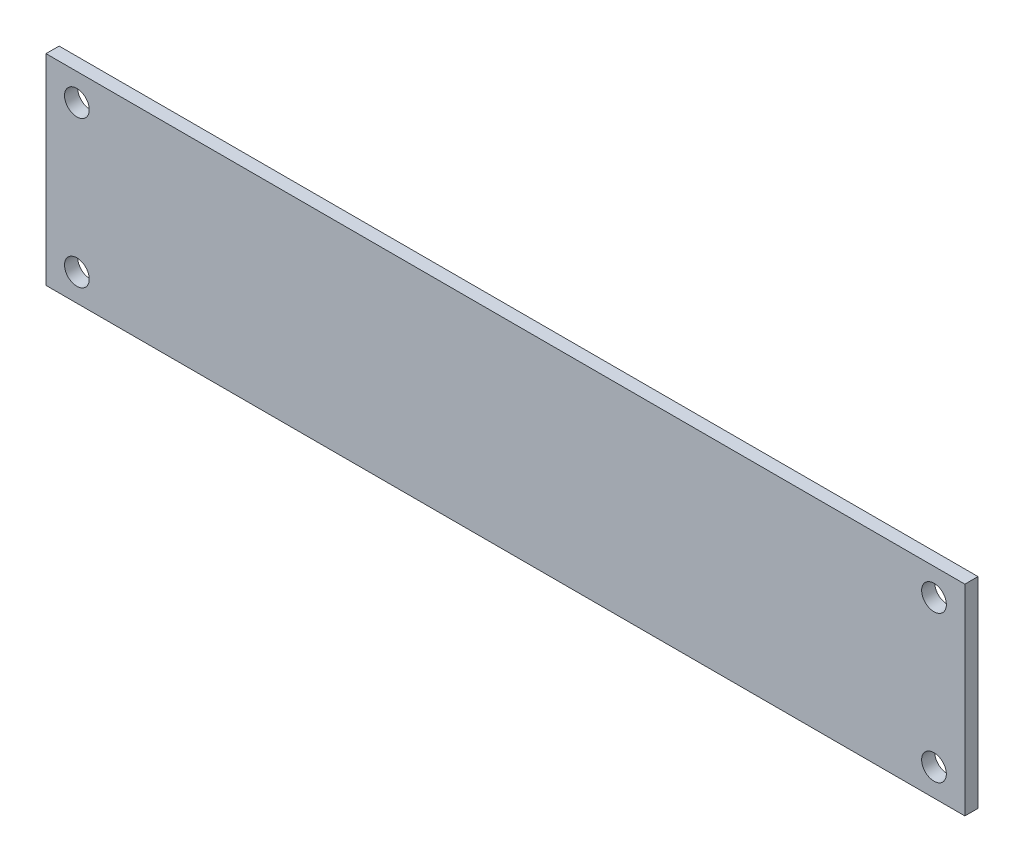
SolidWorks part; units mm, degrees
ref_plane "Front Plane" through (0, 0, 0) normal (0, 0, 1) x (1, 0, 0)
ref_plane "Top Plane" through (0, 0, 0) normal (0, 1, 0) x (1, 0, 0)
ref_plane "Right Plane" through (0, 0, 0) normal (1, 0, 0) x (0, 0, -1)
sketch "Sketch1" plane through (0, 0, 0) normal (0, 0, 1) x (1, 0, 0)
  line L1 (-59.5, 13) -> (59.5, 13)
  line L2 (-59.5, 13) -> (-59.5, -13)
  line L3 (-59.5, -13) -> (59.5, -13)
  line L4 (59.5, 13) -> (59.5, -13)
  circle A0 centre (-55.5, 9.5) radius 1.6
  circle A1 centre (-55.5, -9.5) radius 1.6
  circle A2 centre (55.5, -9.5) radius 1.6
  circle A3 centre (55.5, 9.5) radius 1.6
  point P4 (-59.5, 0)
  point P5 (0, 13)
  point P15 (0, 0)
  point P16 (0, 0)
  point P17 (0, 0)
  point P18 (0, 0)
  point P19 (0, 0)
  dimension "D3" = 3.2
  dimension "D6" = 19
  dimension "D1" = 119
  dimension "D2" = 26
  dimension "D4" = 4
  dimension "D5" = 111
  dimension "D7" = 3.5
extrude "Main" add sketch "Sketch1" along normal blind 1.7
